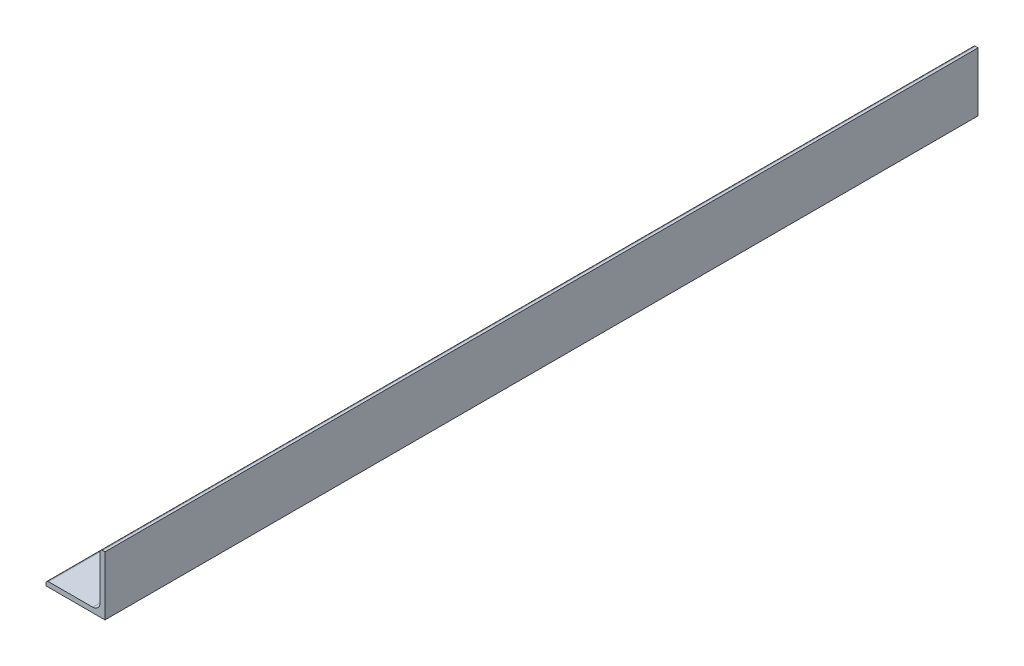
SolidWorks part; units mm, degrees
ref_plane "Front Plane" through (0, 0, 0) normal (0, 0, 1) x (1, 0, 0)
ref_plane "Top Plane" through (0, 0, 0) normal (0, 1, 0) x (1, 0, 0)
ref_plane "Right Plane" through (0, 0, 0) normal (1, 0, 0) x (0, 0, -1)
sketch "Sketch0" plane through (0, 0, 0) normal (0, 0, 1) x (1, 0, 0)
  line L0 (-19.05, -19.05) -> (19.05, -19.05)
  line L1 (19.05, -19.05) -> (19.05, 19.05)
  line L2 (19.05, 0) -> (0, 0) construction
  line L3 (0, 0) -> (0, -19.05) construction
  line L4 (15.875, -11.0998) -> (15.875, 19.05) construction
  line L5 (11.0998, -15.875) -> (-19.05, -15.875) construction
  arc A0 (15.875, -11.0998) -> (11.0998, -15.875) centre (11.0998, -11.0998) cw
  point P3 (14.4764, -14.4764)
  dimension "Inside Corner Radius" = 4.7752
  dimension "Outside Height" = 38.1
  dimension "Inside Height" = 34.925
  dimension "Inside Width" = 34.925
  dimension "Wall Thickness" = 3.175
  dimension "D1" = 3.175
  dimension "Outside Width" = 38.1
sketch "Sketch1" plane through (0, 0, 0) normal (1, 0, 0) x (0, 0, -1)
  line L0 (609.6, 0) -> (-609.6, 0)
  point P4 (0, 0)
  dimension "Length" = 1219.2
sketch "Sketch2" plane through (0, 0, 0) normal (0, 0, 1) x (1, 0, 0)
  line L0 (-19.05, -19.05) -> (19.05, -19.05)
  line L1 (19.05, -19.05) -> (19.05, 19.05)
  line L2 (19.05, 19.05) -> (15.875, 19.05) construction
  line L3 (15.875, 17.4625) -> (15.875, -11.0998)
  line L4 (11.0998, -15.875) -> (-17.4625, -15.875)
  line L5 (-19.05, -19.05) -> (-19.05, -15.875) construction
  line L6 (17.4625, 19.05) -> (19.05, 19.05)
  line L7 (-19.05, -17.4625) -> (-19.05, -19.05)
  line L8 (19.05, 0) -> (0, 0) construction
  line L9 (0, 0) -> (0, -19.05) construction
  arc A0 (15.875, 17.4625) -> (17.4625, 19.05) centre (17.4625, 17.4625) cw
  arc A1 (-19.05, -17.4625) -> (-17.4625, -15.875) centre (-17.4625, -17.4625) cw
  arc A2 (15.875, -11.0998) -> (11.0998, -15.875) centre (11.0998, -11.0998) cw
  dimension "Inside Radius" = 4.7752
  dimension "Height" = 38.1
  dimension "Width" = 38.1
  dimension "Thickness" = 3.175
extrude "Boss-Extrude1" add sketch "Sketch2" along normal mid plane 1219.2
sketch "Break Locations" plane through (0, 0, 0) normal (1, 0, 0) x (0, 0, -1)
  line L0 (-570.738, 0) -> (570.738, 0)
  line L1 (-609.6, -19.05) -> (-609.6, 19.05) construction
  line L2 (609.6, -19.05) -> (609.6, 19.05) construction
  point P0 (-577.215, 0)
  point P1 (577.215, 0)
  point P10 (0, 0)
  point P11 (570.738, 0)
  point P13 (-570.738, 0)
  dimension "D1" = 32.385
  dimension "D2" = 32.385
  dimension "D3" = 38.862
sketch "Sketch3" plane through (19.05, 0, 0) normal (1, 0, 0) x (0, 0, -1)
  line L5 (-609.6, -19.05) -> (609.6, -19.05) construction
  line L6 (609.6, 19.05) -> (-25.6, 19.05)
  line L7 (609.6, 19.05) -> (609.6, -19.05)
  line L8 (609.6, -19.05) -> (-25.6, -19.05)
  line L9 (-25.6, 19.05) -> (-25.6, -19.05)
  line L10 (-609.6, -19.05) -> (-609.6, 19.05) construction
  dimension "D1" = 584
extrude "Cut-Extrude1" cut sketch "Sketch3" against normal blind 60 contours L7 L6 L9 L8
sketch "Sketch4" plane through (19.05, 0, 0) normal (1, 0, 0) x (0, 0, -1)
  line L0 (-609.6, -19.05) -> (-25.6, -19.05) construction
  line L1 (-25.6, 19.05) -> (-45.6, 19.05)
  line L2 (-25.6, 19.05) -> (-25.6, -19.05)
  line L3 (-25.6, -19.05) -> (-45.6, -19.05)
  line L4 (-45.6, 19.05) -> (-45.6, -19.05)
  line L5 (-609.6, -19.05) -> (-609.6, 19.05) construction
  dimension "D1" = 564
extrude "Cut-Extrude2" cut sketch "Sketch4" against normal blind 60 contours L2 L1 L4 L3
equation "\"D1@Break Locations\" = .85 * \"Height@Sketch2\""
equation "\"D2@Break Locations\"=\"D1@Break Locations\""
equation "\"Thickness@Sketch2\" = \"Wall Thickness@Sketch0\""
equation "\"Height@Sketch2\" = \"Outside Height@Sketch0\""
equation "\"Width@Sketch2\" = \"Outside Width@Sketch0\""
equation "\"Inside Radius@Sketch2\" = \"Inside Corner Radius@Sketch0\""
equation "\"Length@Boss-Extrude1\" = \"Length@Sketch1\""
equation "\"D3@Break Locations\"=\"D2@Break Locations\"*1.2"
equation "\"D1@Sketch0\"=\"Wall Thickness@Sketch0\""
